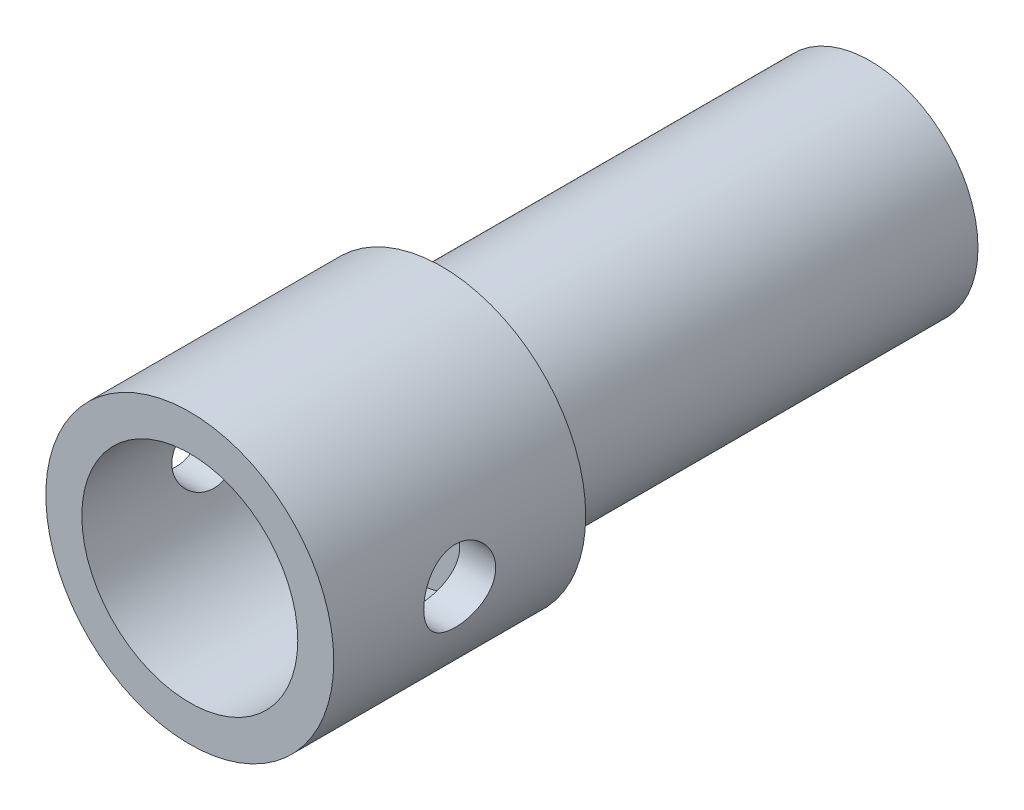
SolidWorks part; units mm, degrees
ref_plane "Front Plane" through (0, 0, 0) normal (0, 0, 1) x (1, 0, 0)
ref_plane "Top Plane" through (0, 0, 0) normal (0, 1, 0) x (1, 0, 0)
ref_plane "Right Plane" through (0, 0, 0) normal (1, 0, 0) x (0, 0, -1)
sketch "Sketch1" plane through (0, 0, 0) normal (0, 0, 1) x (1, 0, 0)
  circle A0 centre (0, 0) radius 40
  circle A1 centre (0, 0) radius 30
  dimension "D1" = 80
  dimension "D2" = 60
extrude "Boss-Extrude1" add sketch "Sketch1" against normal blind 70
sketch "Sketch2" plane through (0, 0, -70) normal (0, 0, -1) x (-1, 0, 0)
  circle A0 centre (0, 0) radius 30
extrude "Boss-Extrude2" add sketch "Sketch2" along normal blind 119 and the other way blind 10
sketch "Sketch3" plane through (0, 0, -189) normal (0, 0, -1) x (-1, 0, 0)
  circle A0 centre (0, 0) radius 25
  dimension "D1" = 50
sketch "Sketch4" plane through (0, 0, -189) normal (0, 0, -1) x (-1, 0, 0)
  line L1 (8.5, -14.7224) -> (17, 0)
  line L2 (17, 0) -> (8.5, 14.7224)
  line L3 (8.5, 14.7224) -> (-8.5, 14.7224)
  line L4 (-8.5, 14.7224) -> (-17, 0)
  line L5 (-17, 0) -> (-8.5, -14.7224)
  line L6 (-8.5, -14.7224) -> (8.5, -14.7224)
  circle A0 centre (0, 0) radius 14.7224 construction
  dimension "D1" = 17
extrude "Cut-Extrude1" cut sketch "Sketch4" against normal blind 20
sketch "Sketch5" plane through (0, 0, 0) normal (1, 0, 0) x (0, 0, -1)
  line L0 (70, 40) -> (0, 40) construction
  line L1 (0, 40) -> (70, 40) construction
  line L2 (70, -40) -> (70, 40) construction
  line L3 (0, 40) -> (0, -40) construction
  circle A0 centre (35, 0) radius 10
  dimension "D1" = 20
  dimension "D2" = 35
extrude "Cut-Extrude2" cut sketch "Sketch5" against normal mid plane 110
